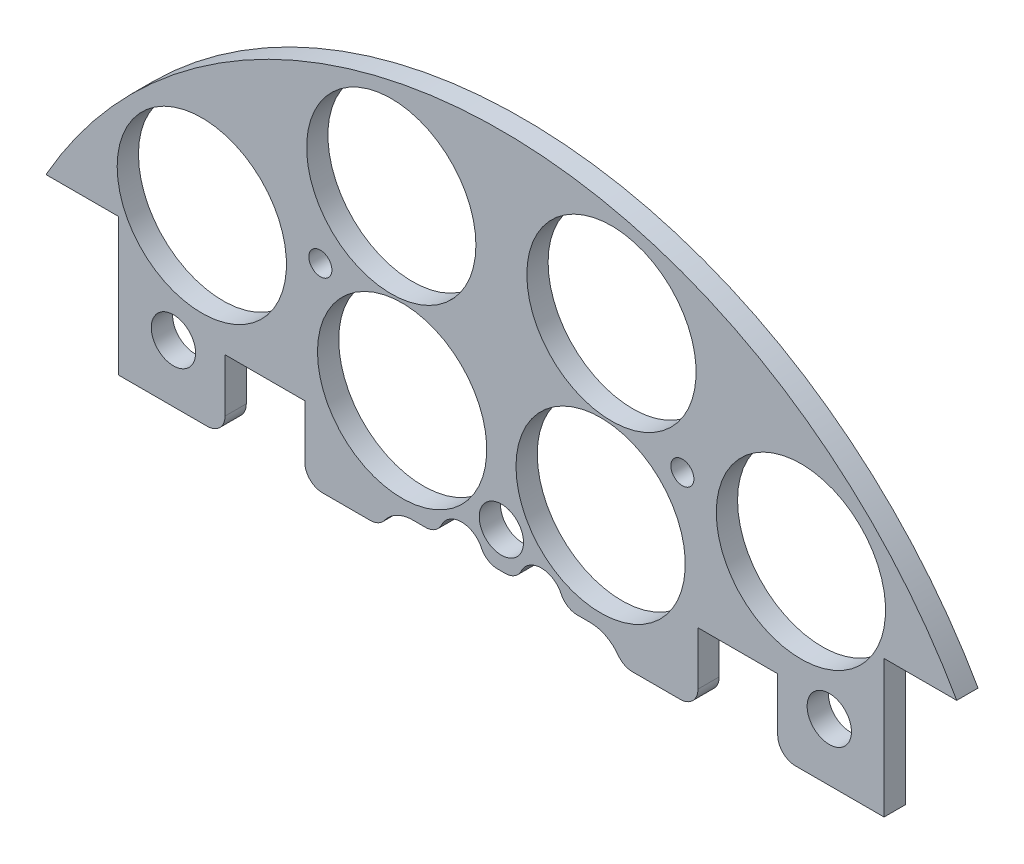
SolidWorks part; units mm, degrees
ref_plane "Front Plane" through (0, 0, 0) normal (0, 0, 1) x (1, 0, 0)
ref_plane "Top Plane" through (0, 0, 0) normal (0, 1, 0) x (1, 0, 0)
ref_plane "Right Plane" through (0, 0, 0) normal (1, 0, 0) x (0, 0, -1)
sketch "Sketch1" plane through (0, 0, 0) normal (0, 0, 1) x (1, 0, 0)
  line L0 (0, 0) -> (-82.1241, 0) construction
  line L1 (0, 0) -> (0, 95.6219) construction
  line L3 (-65.2538, 36.83) -> (-54.8398, 36.83)
  line L5 (-65.2538, -36.83) -> (-54.8398, -36.83)
  line L6 (-54.8398, 36.83) -> (-54.8398, -36.83)
  line L7 (65.2538, -36.83) -> (54.8398, -36.83)
  line L8 (65.2538, 36.83) -> (54.8398, 36.83)
  line L9 (54.8398, 36.83) -> (54.8398, -36.83)
  arc A0 (-65.2538, -36.83) -> (65.2538, -36.83) centre (0, 0) ccw
  circle A1 centre (-45.466, 11.049) radius 1.651
  circle A2 centre (-20.0673, 10.795) radius 1.651
  circle A3 centre (-20.0673, -10.795) radius 1.651
  circle A4 centre (-45.466, -11.049) radius 1.651
  circle A5 centre (45.466, -11.049) radius 1.651
  circle A6 centre (20.0673, -10.795) radius 1.651
  circle A7 centre (20.0673, 10.795) radius 1.651
  circle A8 centre (45.466, 11.049) radius 1.651
  arc A9 (65.2538, 36.83) -> (-65.2538, 36.83) centre (0, 0) ccw
  dimension "D2" = 3.302
  dimension "D3" = 3.302
  dimension "D4" = 25.4
  dimension "D5" = 10.795
  dimension "D10" = 45.466
  dimension "D6" = 73.66
  dimension "D7" = 10.414
  dimension "D8" = 74.93
  dimension "D9" = 74.93
  dimension "D11" = 36.83
extrude "Boss-Extrude2" add sketch "Sketch1" along normal blind 3.048
sketch "Sketch2" plane through (0, 0, 3.048) normal (0, 0, 1) x (1, 0, 0)
  line L0 (0, 68.58) -> (0, 55.88) construction
  line L1 (-9.525, 68.58) -> (9.525, 68.58)
  line L2 (-9.525, 68.58) -> (-9.525, 55.88)
  line L3 (-9.525, 55.88) -> (9.525, 55.88)
  line L4 (9.525, 68.58) -> (9.525, 55.88)
  line L5 (-9.525, 62.23) -> (9.525, 62.23) construction
  arc A0 (65.2538, 36.83) -> (-65.2538, 36.83) centre (0, 0) ccw construction
  circle A1 centre (-20.0673, 10.795) radius 1.651 construction
  circle A2 centre (20.0673, 10.795) radius 1.651 construction
  circle A3 centre (-6.731, 62.23) radius 1.143
  circle A4 centre (6.731, 62.23) radius 1.143
  dimension "D4" = 2.286
  dimension "D5" = 0
  dimension "D6" = 6.731
  dimension "D1" = 19.05
  dimension "D2" = 12.7
  dimension "D3" = 55.88
extrude "Cut-Extrude1" cut sketch "Sketch2" against normal through all contours A3 | A4
sketch "Sketch3" plane through (0, 0, 0) normal (0, 0, -1) x (-1, 0, 0)
  line L0 (0, 0) -> (0, -116.2908) construction
  line L1 (0, 0) -> (-153.8039, 0) construction
  line L3 (0, 0) -> (12.9121, -31.1274) construction
  circle A4 centre (-42.926, -42.926) radius 12.1285
  circle A5 centre (-14.224, 34.29) radius 12.1285
  circle A6 centre (14.224, -34.29) radius 12.1285
  circle A7 centre (14.224, 34.29) radius 12.1285
  circle A8 centre (-42.926, 42.926) radius 12.1285
  circle A11 centre (42.926, 42.926) radius 12.1285
  circle A13 centre (-14.224, -34.29) radius 12.1285
  circle A14 centre (42.926, -42.926) radius 12.1285
  point P36 (0, 0)
  point P53 (0, 0)
  point P55 (0, 0)
  dimension "D1" = 34.29
  dimension "D2" = 14.224
  dimension "D3" = 42.926
  dimension "D4" = 42.926
  dimension "D6" = 0
extrude "Cut-Extrude2" cut sketch "Sketch3" against normal through all
sketch "Sketch4" plane through (0, 0, 0) normal (0, 0, -1) x (-1, 0, 0)
  line L1 (-15.7702, 56.3138) -> (12.7925, 56.3138)
  line L2 (-15.7702, 56.3138) -> (-15.7702, 67.9913)
  line L3 (-15.7702, 67.9913) -> (12.7925, 67.9913)
  line L4 (12.7925, 56.3138) -> (12.7925, 67.9913)
extrude "Boss-Extrude3" add sketch "Sketch4" against normal up to surface (3.048 mm away) up to face at (-55.0545, -42.926, 3.048)
sketch "Sketch5" plane through (0, 0, 0) normal (0, 0, -1) x (-1, 0, 0)
  line L1 (-113.3786, -90.442) -> (117.3207, -90.442)
  line L2 (-113.3786, -90.442) -> (-113.3786, 17.145)
  line L3 (-113.3786, 17.145) -> (117.3207, 17.145)
  line L4 (117.3207, -90.442) -> (117.3207, 17.145)
  circle A1 centre (20.0673, 10.795) radius 1.651 construction
  dimension "D1" = 6.35
extrude "Cut-Extrude3" cut sketch "Sketch5" against normal through all
sketch "Sketch6" plane through (0, 0, 0) normal (0, 0, -1) x (-1, 0, 0)
  line L0 (0, 0) -> (0, 74.93) construction
  line L1 (0, 0) -> (-15.5068, 57.8721) construction
  arc A0 (65.2538, 36.83) -> (-65.2538, 36.83) centre (0, 0) ccw construction
  circle A1 centre (-15.7776, 58.8828) radius 12.1285
  circle A3 centre (15.7776, 58.8828) radius 12.1285
  dimension "D1" = 24.257
  dimension "D2" = 0
  dimension "D4" = 60.96
  dimension "D3" = 15
extrude "Cut-Extrude4" cut sketch "Sketch6" against normal through all
extrude "Cut-Extrude5" cut sketch "Sketch7" against normal through all both and the other way through all
sketch "Sketch7" plane through (31.3134, 132.614, -9.525) normal (0, 0, -1) x (0, 1, 0)
  line L0 (-132.614, -31.3134) -> (-132.614, 57.8454) construction
  line L1 (-132.614, -31.3134) -> (-222.516, -31.3134) construction
  circle A0 centre (-158.014, 14.4066) radius 3.175
  circle A1 centre (-173.254, -31.3134) radius 3.175
  circle A3 centre (-158.014, -77.0334) radius 3.175
  circle A4 centre (-107.214, -77.0334) radius 3.175
  circle A5 centre (-91.974, -31.3134) radius 3.175
  circle A6 centre (-107.214, 14.4066) radius 3.175
extrude "Cut-Extrude6" cut sketch "Sketch8" against normal blind 29.21
sketch "Sketch8" plane through (31.3134, 132.559, -6.35) normal (0, 0, -1) x (0, 1, 0)
  line L0 (-132.559, -31.3134) -> (6.1626, -31.3134) construction
  line L2 (-132.559, -31.3134) -> (-132.559, -122.6589) construction
  circle A0 centre (-190.979, 2.9766) radius 1.651
  circle A2 centre (-154.784, -31.3134) radius 1.651
  circle A3 centre (-190.979, -65.6034) radius 1.651
  circle A4 centre (-110.334, -31.3134) radius 1.651
  circle A5 centre (-74.139, -65.6034) radius 1.651
  circle A6 centre (-74.139, 2.9766) radius 1.651
sketch "Sketch9" plane through (0, 0, 0) normal (0, 0, -1) x (-1, 0, 0)
  line L0 (54.8398, 17.145) -> (-54.8398, 17.145) construction
  line L1 (39.5998, 17.145) -> (28.1698, 17.145)
  line L2 (39.5998, 17.145) -> (39.5998, 27.305)
  line L3 (39.5998, 27.305) -> (28.1698, 27.305)
  line L4 (28.1698, 17.145) -> (28.1698, 27.305)
  line L5 (54.8398, 36.83) -> (54.8398, 17.145) construction
  line L6 (-28.1698, 17.145) -> (-39.5998, 17.145)
  line L7 (-28.1698, 17.145) -> (-28.1698, 27.305)
  line L8 (-28.1698, 27.305) -> (-39.5998, 27.305)
  line L9 (-39.5998, 17.145) -> (-39.5998, 27.305)
  line L10 (0, -5.7413) -> (0, 83.8896) construction
  dimension "D1" = 10.16
  dimension "D2" = 11.43
  dimension "D3" = 15.24
extrude "Cut-Extrude7" cut sketch "Sketch9" against normal through all
extrude "Cut-Extrude63" cut sketch "Sketch65" against normal blind 97.79
sketch "Sketch65" plane through (30.092, 4.0835, -16.1925) normal (0, 0, -1) x (-1, 0, 0)
  line L0 (30.092, -29.4835) -> (30.092, 6.2385) construction
  circle A0 centre (4.1544, -49.7288) radius 1.651
  circle A4 centre (56.0296, -49.7288) radius 1.651
  circle A5 centre (4.1544, 41.3825) radius 1.651
  circle A9 centre (56.0296, 41.3825) radius 1.651
extrude "Cut-Extrude117" cut sketch "Sketch119" against normal blind 48.768 and the other way blind 103.378
sketch "Sketch119" plane through (30.092, 4.0835, 19.939) normal (0, 0, -1) x (-1, 0, 0)
  line L0 (30.092, -4.0835) -> (148.6336, -4.0835) construction
  line L1 (30.092, -4.0835) -> (30.092, 90.452) construction
  circle A0 centre (-16.898, 21.3165) radius 3.175
  circle A1 centre (77.082, 21.3165) radius 3.175
  circle A2 centre (30.092, 21.3165) radius 3.175
  circle A4 centre (77.082, -29.4835) radius 3.175
  circle A5 centre (30.092, -29.4835) radius 3.175
  circle A6 centre (-16.898, -29.4835) radius 3.175
sketch "Sketch12" plane through (0, 0, 0) normal (0, 0, -1) x (-1, 0, 0)
  line L0 (0, 0) -> (0, 13.6061) construction
  line L1 (12.7, 20.24) -> (8.889, 20.24)
  line L2 (7.7, 15.24) -> (-7.7, 15.24)
  line L3 (-8.889, 20.24) -> (-12.7, 20.24)
  line L4 (2.541, 20.24) -> (-2.541, 20.24)
  arc A0 (7.7, 15.24) -> (12.7, 20.24) centre (12.7, 15.24) ccw
  arc A1 (-7.7, 15.24) -> (-12.7, 20.24) centre (-12.7, 15.24) cw
  arc A2 (8.889, 20.24) -> (2.541, 20.24) centre (5.715, 20.32) ccw
  arc A3 (-2.541, 20.24) -> (-8.889, 20.24) centre (-5.715, 20.32) ccw
  dimension "D1" = 10
  dimension "D4" = 6.35
  dimension "D5" = 6.35
  dimension "D2" = 15.24
  dimension "D3" = 12.7
  dimension "D6" = 11.43
  dimension "D7" = 20.32
  dimension "D8" = 5.715
extrude "Cut-Extrude10" cut sketch "Sketch12" against normal blind 14.224
fillet "Fillet1" radius 2.54 10 edges at (39.5998, 17.145, 1.524) (28.1698, 17.145, 1.524) (17.3229, 17.145, 1.524) (8.889, 20.24, 1.524) (2.541, 20.24, 1.524) (-2.541, 20.24, 1.524) (-8.889, 20.24, 1.524) (-17.3229, 17.145, 1.524) (-28.1698, 17.145, 1.524) (-39.5998, 17.145, 1.524)
